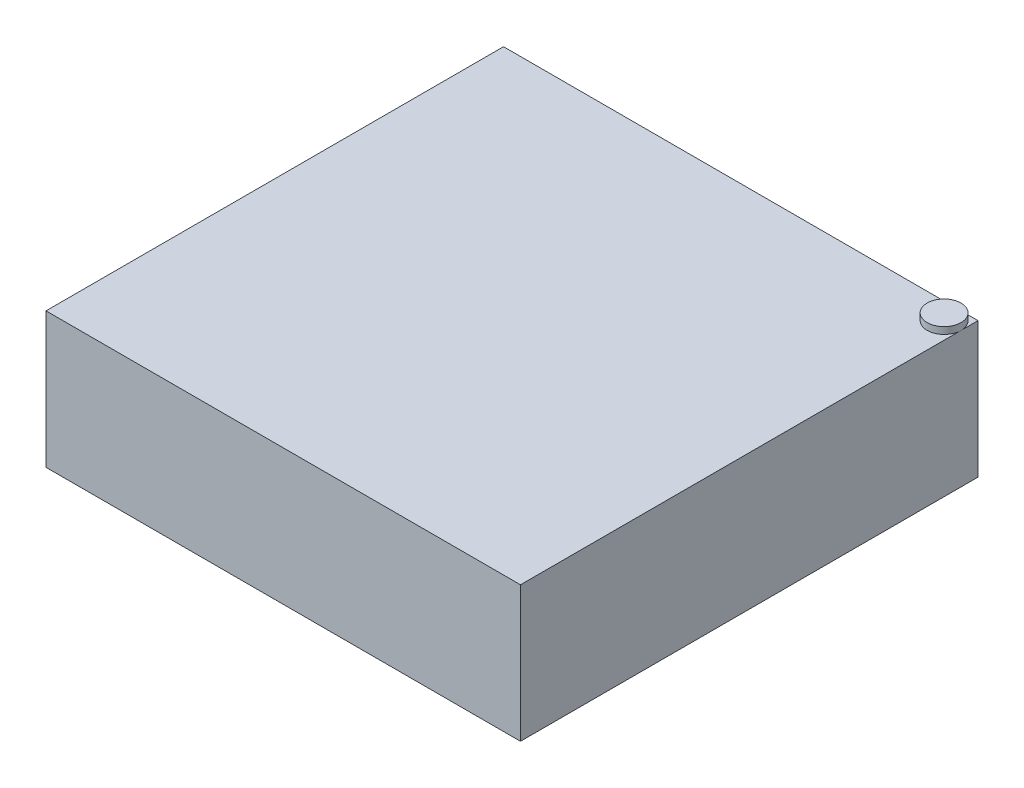
SolidWorks part; units mm, degrees
ref_plane "Front Plane" through (0, 0, 0) normal (0, 0, 1) x (1, 0, 0)
ref_plane "Top Plane" through (0, 0, 0) normal (0, 1, 0) x (1, 0, 0)
ref_plane "Right Plane" through (0, 0, 0) normal (1, 0, 0) x (0, 0, -1)
sketch "Sketch1" plane through (0, 0, 0) normal (0, 1, 0) x (1, 0, 0)
  line L1 (-88.9, -85.725) -> (88.9, -85.725)
  line L2 (-88.9, -85.725) -> (-88.9, 85.725)
  line L3 (-88.9, 85.725) -> (88.9, 85.725)
  line L4 (88.9, -85.725) -> (88.9, 85.725)
  line L5 (-88.9, -85.725) -> (88.9, 85.725) construction
  line L6 (-88.9, 85.725) -> (88.9, -85.725) construction
  point P0 (0, 0)
  dimension "D1" = 177.8
  dimension "D2" = 171.45
extrude "Boss-Extrude1" add sketch "Sketch1" along normal blind 50.8
sketch "Sketch2" plane through (0, 50.8, 0) normal (0, 1, 0) x (1, 0, 0)
  line L0 (88.9, 85.725) -> (-88.9, 85.725) construction
  line L1 (88.9, -85.725) -> (88.9, 85.725) construction
  circle A0 centre (82.55, 79.375) radius 6.35
  dimension "D1" = 12.7
  dimension "D2" = 6.35
  dimension "D3" = 6.35
extrude "Boss-Extrude2" add sketch "Sketch2" along normal blind 2.54
